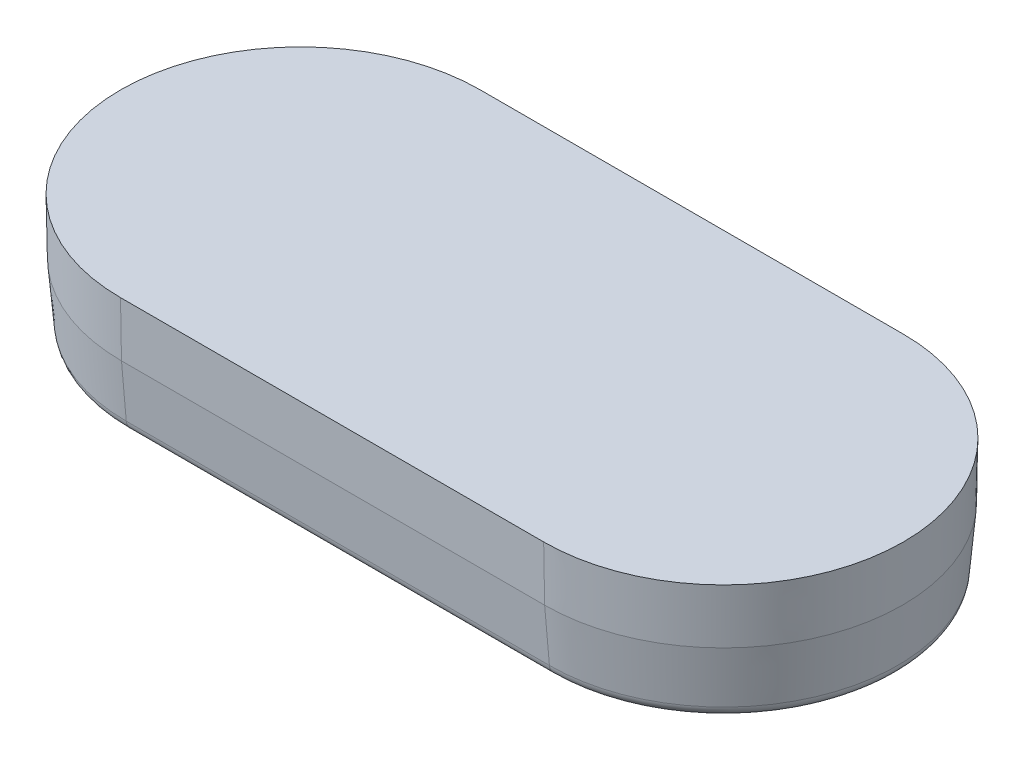
SolidWorks part; units mm, degrees
material "CA"
ref_plane "Front Plane" through (0, 0, 0) normal (0, 0, 1) x (1, 0, 0)
ref_plane "Top Plane" through (0, 0, 0) normal (0, 1, 0) x (1, 0, 0)
ref_plane "Right Plane" through (0, 0, 0) normal (1, 0, 0) x (0, 0, -1)
sketch "Sketch1" plane through (0, 0, 0) normal (0, 1, 0) x (1, 0, 0)
  line L0 (-11.1125, 0) -> (11.1125, 0) construction
  line L1 (-11.1125, 9.4488) -> (11.1125, 9.4488)
  line L2 (-11.1125, -9.4488) -> (11.1125, -9.4488)
  arc A0 (-11.1125, 9.4488) -> (-11.1125, -9.4488) centre (-11.1125, 0) ccw
  arc A1 (11.1125, -9.4488) -> (11.1125, 9.4488) centre (11.1125, 0) ccw
  point P2 (0, 0)
  dimension "D1" = 18.8976
  dimension "D2" = 41.1226
extrude "Boss-Extrude1" add sketch "Sketch1" against normal blind 6.35 draft 1
sketch "Sketch6" plane through (0, 0, 0) normal (0, 0, 1) x (1, 0, 0)
  line L0 (0, 0) -> (0, -1.5875) construction
  line L1 (0, -1.5875) -> (-7.9375, -9.525)
  line L2 (0, -1.5875) -> (7.9375, -9.525)
  line L3 (-7.9375, -9.525) -> (7.9375, -9.525)
  line L5 (11.1125, 0) -> (-11.1125, 0) construction
  dimension "D1" = 1.5875
  dimension "D2" = 90
  dimension "D3" = 9.525
extrude "Cut-Extrude3" cut sketch "Sketch6" against normal through all and the other way through all
pattern_linear "LPattern1" count 12 spacing 3.175 along (1, 0, 0) count 8 spacing 3.175 along (-1, 0, 0) of "Cut-Extrude3"
sketch "Sketch7" plane through (0, 0, 0) normal (0, 1, 0) x (1, 0, 0)
  line L2 (-11.1125, -9.4488) -> (11.1125, -9.4488)
  line L3 (-11.1125, -9.4488) -> (11.1125, -9.4488)
  line L4 (11.1125, 9.4488) -> (-11.1125, 9.4488)
  line L5 (11.1125, 9.4488) -> (-11.1125, 9.4488)
  line L6 (-11.1125, -7.2898) -> (11.1125, -7.2898)
  line L7 (-11.1125, -7.2898) -> (11.1125, -7.2898)
  line L8 (11.1125, 7.2898) -> (-11.1125, 7.2898)
  line L9 (11.1125, 7.2898) -> (-11.1125, 7.2898)
  arc A1 (-11.1125, 9.4488) -> (-11.1125, -9.4488) centre (-11.1125, 0) ccw
  arc A2 (-11.1125, 9.4488) -> (-11.1125, -9.4488) centre (-11.1125, 0) ccw
  arc A3 (-11.1125, 7.2898) -> (-11.1125, -7.2898) centre (-11.1125, 0) ccw
  arc A4 (-11.1125, 7.2898) -> (-11.1125, -7.2898) centre (-11.1125, 0) ccw
  arc A6 (11.1125, -9.4488) -> (11.1125, 9.4488) centre (11.1125, 0) ccw
  arc A7 (11.1125, -9.4488) -> (11.1125, 9.4488) centre (11.1125, 0) ccw
  arc A8 (11.1125, -7.2898) -> (11.1125, 7.2898) centre (11.1125, 0) ccw
  arc A9 (11.1125, -7.2898) -> (11.1125, 7.2898) centre (11.1125, 0) ccw
  dimension "D1" = 0
  dimension "D2" = 2.159
extrude "Boss-Extrude3" add sketch "Sketch7" against normal blind 6.35 draft 1
sketch "Sketch8" plane through (0, 0, 0) normal (0, 1, 0) x (1, 0, 0)
  line L2 (-11.1125, -9.652) -> (11.1125, -9.652)
  line L3 (-11.1125, -9.652) -> (11.1125, -9.652)
  line L4 (11.1125, 9.652) -> (-11.1125, 9.652)
  line L5 (11.1125, 9.652) -> (-11.1125, 9.652)
  arc A2 (-11.1125, 9.652) -> (-11.1125, -9.652) centre (-11.1125, 0) ccw
  arc A3 (-11.1125, 9.652) -> (-11.1125, -9.652) centre (-11.1125, 0) ccw
  arc A4 (11.1125, -9.652) -> (11.1125, 9.652) centre (11.1125, 0) ccw
  arc A5 (11.1125, -9.652) -> (11.1125, 9.652) centre (11.1125, 0) ccw
  dimension "D1" = 0.2032
extrude "Cut-Extrude4" cut sketch "Sketch8" against normal through all draft 5 flip side to cut draft outward yes
draft "Draft2" type of draft neutral plane draft angle 5 faces to draft 4 face at (-14.479, -3.1025, 0) face at (0, -2.8949, -7.3403) face at (14.479, -3.1025, 0) face at (0, -2.8949, 7.3403) neutral plane through (-11.1125, 0, 0) neutral plane normal (0, 1, 0) reverse direction yes parameters "D1"=5
fillet "Fillet2" radius 0.635 8 edges at (-18.9579, -6.35, 0) (0, -6.35, -7.8454) (18.9579, -6.35, 0) (-20.2089, -6.35, 0) (0, -6.35, -9.0964) (20.2089, -6.35, 0) (0, -6.35, 7.8454) (0, -6.35, 9.0964)
sketch "Sketch11 - OFFSET .005" plane through (0, 0, 0) normal (0, 1, 0) x (1, 0, 0)
  line L2 (-11.1125, -9.5758) -> (11.1125, -9.5758)
  line L3 (-11.1125, -9.5758) -> (11.1125, -9.5758)
  line L4 (11.1125, 9.5758) -> (-11.1125, 9.5758)
  line L5 (11.1125, 9.5758) -> (-11.1125, 9.5758)
  arc A1 (-11.1125, 9.5758) -> (-11.1125, -9.5758) centre (-11.1125, 0) ccw
  arc A2 (-11.1125, 9.5758) -> (-11.1125, -9.5758) centre (-11.1125, 0) ccw
  arc A4 (11.1125, -9.5758) -> (11.1125, 9.5758) centre (11.1125, 0) ccw
  arc A5 (11.1125, -9.5758) -> (11.1125, 9.5758) centre (11.1125, 0) ccw
  dimension "D1" = 0.127
